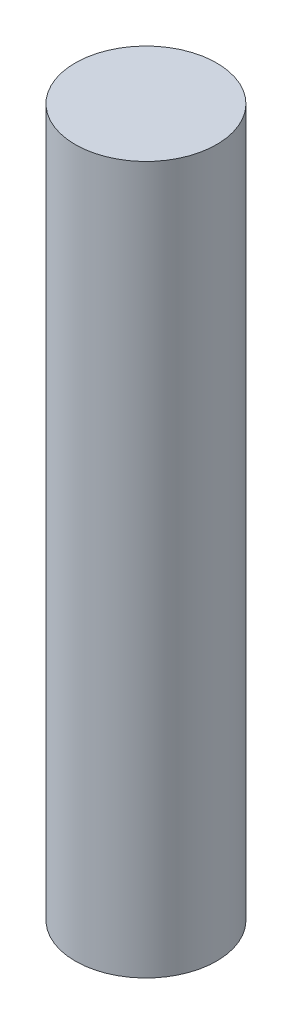
SolidWorks part; units mm, degrees
ref_plane "Front Plane" through (0, 0, 0) normal (0, 0, 1) x (1, 0, 0)
ref_plane "Top Plane" through (0, 0, 0) normal (0, 1, 0) x (1, 0, 0)
ref_plane "Right Plane" through (0, 0, 0) normal (1, 0, 0) x (0, 0, -1)
sketch "Sketch1" plane through (0, 0, 0) normal (0, 1, 0) x (1, 0, 0)
  circle A0 centre (0, 0) radius 2.286
  dimension "D1" = 4.572
extrude "Boss-Extrude1" add sketch "Sketch1" along normal blind 22.86
